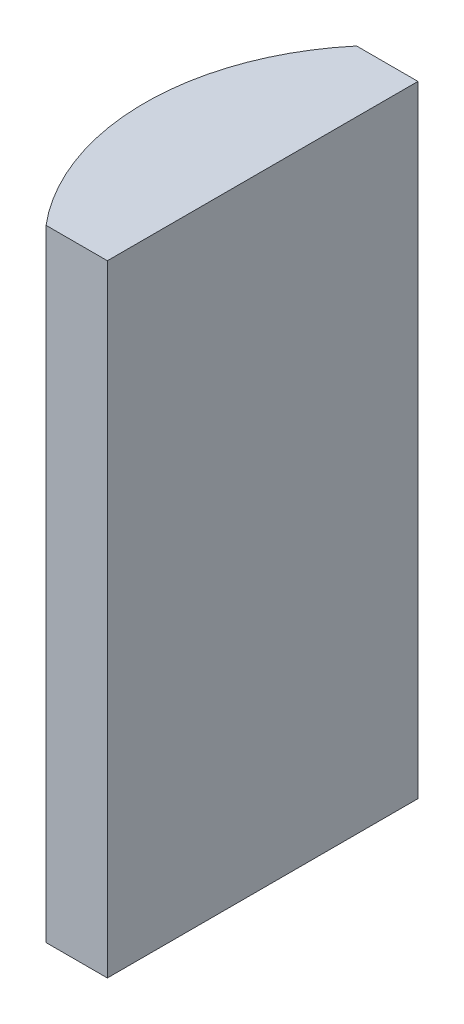
SolidWorks part; units mm, degrees
ref_plane "前视基准面" through (0, 0, 0) normal (0, 0, 1) x (1, 0, 0)
ref_plane "上视基准面" through (0, 0, 0) normal (0, 1, 0) x (1, 0, 0)
ref_plane "右视基准面" through (0, 0, 0) normal (1, 0, 0) x (0, 0, -1)
sketch "草图1" plane through (0, 0, 0) normal (0, 1, 0) x (1, 0, 0)
  line L0 (10.7432, 0) -> (-19.1624, 0) construction
  line L1 (-1.5792, 5) -> (0.3952, 5)
  line L2 (-1.5792, -5) -> (0.3952, -5)
  line L3 (0.3952, 5) -> (0.3952, -5)
  arc A0 (-1.5792, 5) -> (-1.5792, -5) centre (4.3552, 0) ccw
  point P19 (-3.4048, 0)
  point P20 (0.3952, 0)
  dimension "D2" = 5
  dimension "D3" = 7.76
  dimension "D4" = 3.8
  dimension "D1" = 5
extrude "凸台-拉伸1" add sketch "草图1" along normal blind 20
